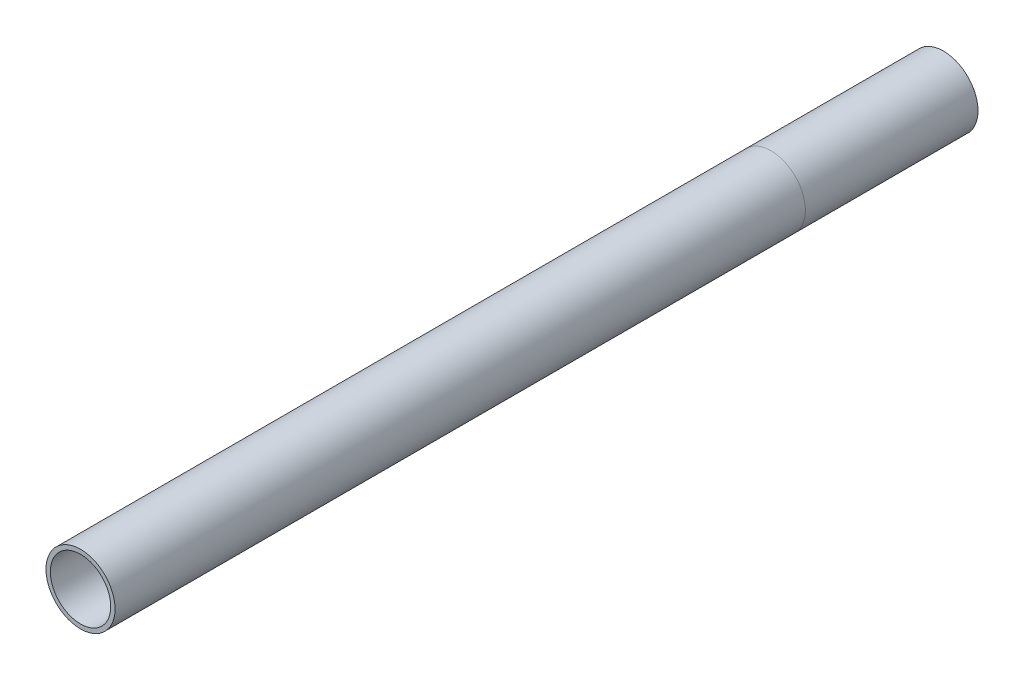
SolidWorks part; units mm, degrees
ref_plane "Ön Düzlem" through (0, 0, 0) normal (0, 0, 1) x (1, 0, 0)
ref_plane "Üst Düzlem" through (0, 0, 0) normal (0, 1, 0) x (1, 0, 0)
ref_plane "Sağ Düzlem" through (0, 0, 0) normal (1, 0, 0) x (0, 0, -1)
sketch "Sketch1" plane through (0, 0, 0) normal (0, 0, 1) x (1, 0, 0)
  circle A0 centre (0, 0) radius 8
  circle A2 centre (0, 0) radius 7
  dimension "D1" = 16
  dimension "D2" = 1
extrude "Boss-Extrude1" add sketch "Sketch1" along normal blind 200
sketch "Sketch2" plane through (0, 0, 0) normal (0, 1, 0) x (1, 0, 0)
  line L0 (-15, -40) -> (15, -40)
  point P4 (0, -40)
  dimension "D1" = 40
  dimension "D2" = 30
split line "Split Line2"
equation "\"motor_r\"= 35 / 2mm"
equation "\"boru_d\"= 16mm"
equation "\"D1@Sketch1\"=\"boru_d\""
